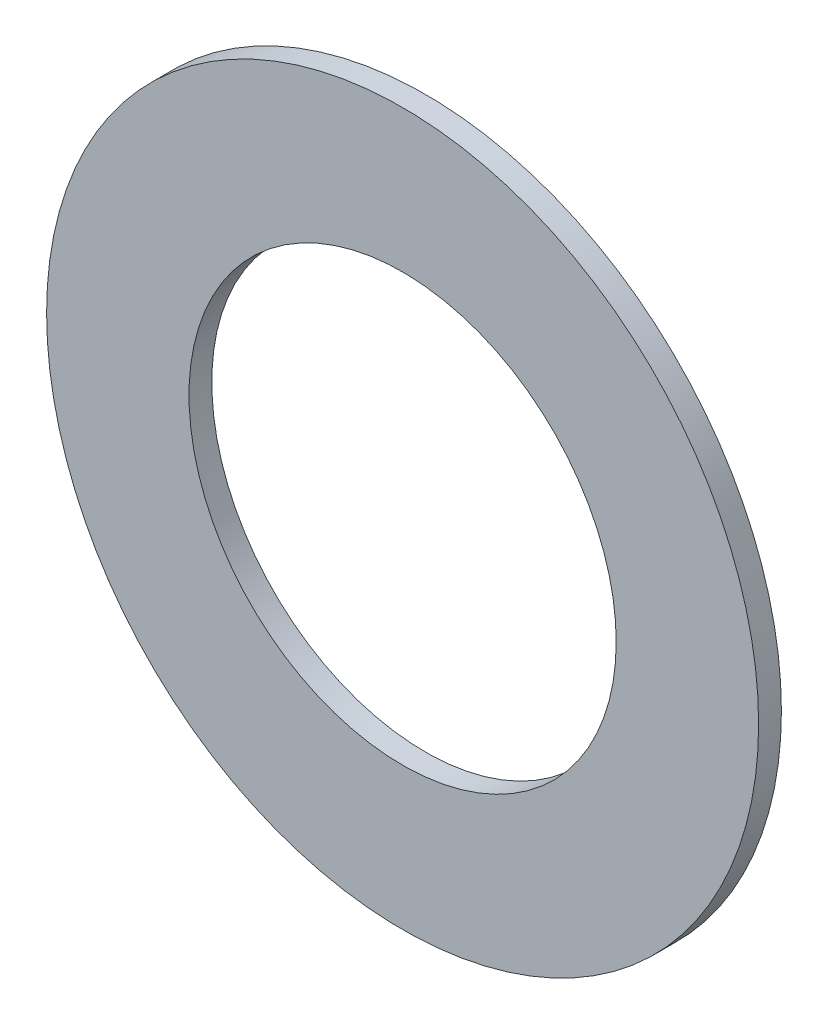
SolidWorks part; units mm, degrees
ref_plane "Front" through (0, 0, 0) normal (0, 0, 1) x (1, 0, 0)
ref_plane "Top" through (0, 0, 0) normal (0, 1, 0) x (1, 0, 0)
ref_plane "Right" through (0, 0, 0) normal (1, 0, 0) x (0, 0, -1)
sketch "face" plane through (0, 0, 0) normal (0, 0, 1) x (1, 0, 0)
  circle A0 centre (0, 0) radius 7.9375
  circle A1 centre (0, 0) radius 4.7625
  dimension "OD" = 15.875
  dimension "ID" = 9.525
extrude "washer" add sketch "face" against normal blind 0.508
